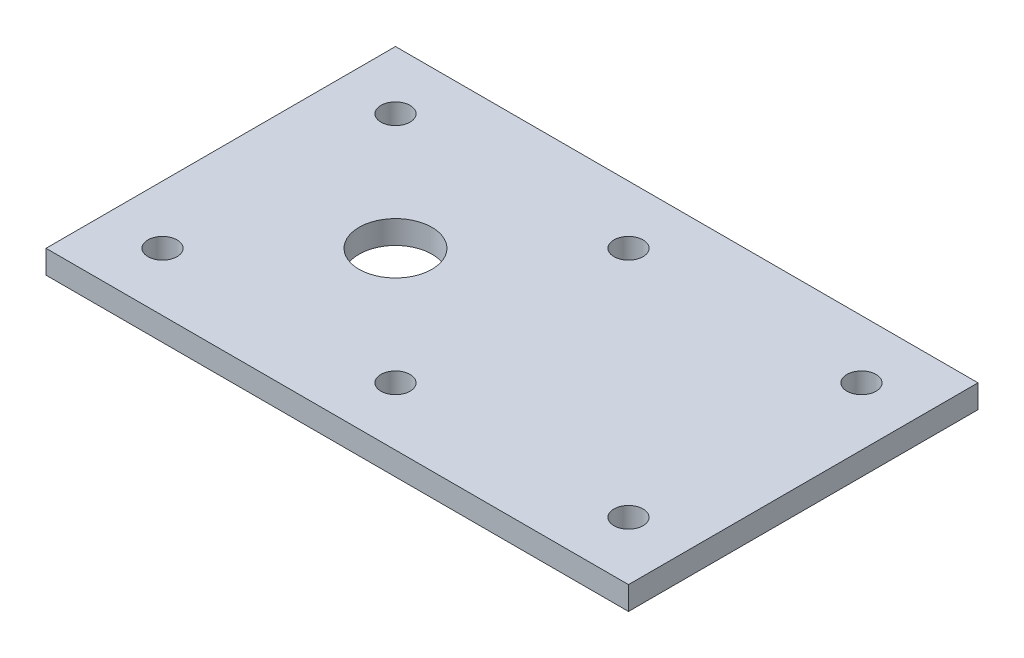
SolidWorks part; units mm, degrees
ref_plane "Front Plane" through (0, 0, 0) normal (0, 0, 1) x (1, 0, 0)
ref_plane "Top Plane" through (0, 0, 0) normal (0, 1, 0) x (1, 0, 0)
ref_plane "Right Plane" through (0, 0, 0) normal (1, 0, 0) x (0, 0, -1)
sketch "Sketch2" plane through (0, 0, 0) normal (0, 1, 0) x (1, 0, 0)
  line L0 (-60, 0) -> (140, 0) construction
  line L1 (-60, 60) -> (140, 60)
  line L2 (-60, 60) -> (-60, -60)
  line L3 (-60, -60) -> (140, -60)
  line L4 (140, 60) -> (140, -60)
  dimension "D1" = 120
  dimension "D2" = 200
  dimension "D3" = 60
extrude "Boss-Extrude3" add sketch "Sketch2" along normal blind 8
sketch "Sketch3" plane through (0, 8, 0) normal (0, 1, 0) x (1, 0, 0)
  line L1 (-60, 60) -> (-60, -60) construction
  line L3 (140, 60) -> (-60, 60) construction
  circle A0 centre (-40, 40) radius 5
  dimension "D3" = 10
  dimension "D1" = 20
  dimension "D2" = 20
extrude "Cut-Extrude1" cut sketch "Sketch3" against normal through all
pattern_linear "LPattern2" count 2 spacing 80 along (0, 0, 1) count 3 spacing 80 along (1, 0, 0) of "Cut-Extrude1"
sketch "Sketch4" plane through (0, 8, 0) normal (0, 1, 0) x (1, 0, 0)
  circle A0 centre (0, 0) radius 12.5
  dimension "D1" = 25
extrude "Cut-Extrude2" cut sketch "Sketch4" against normal blind 10 contours A0
